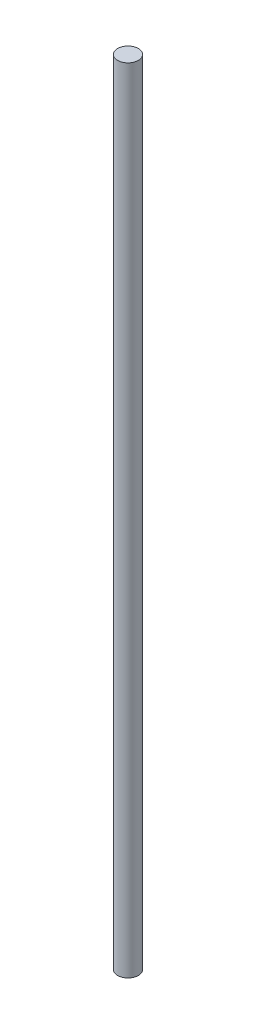
SolidWorks part; units mm, degrees
ref_plane "Front Plane" through (0, 0, 0) normal (0, 0, 1) x (1, 0, 0)
ref_plane "Top Plane" through (0, 0, 0) normal (0, 1, 0) x (1, 0, 0)
ref_plane "Right Plane" through (0, 0, 0) normal (1, 0, 0) x (0, 0, -1)
sketch "Sketch1" plane through (0, 0, 0) normal (0, 1, 0) x (1, 0, 0)
  circle A0 centre (0, 0) radius 0.3
  dimension "D1" = 0.6
extrude "Boss-Extrude1" add sketch "Sketch1" along normal blind 23
